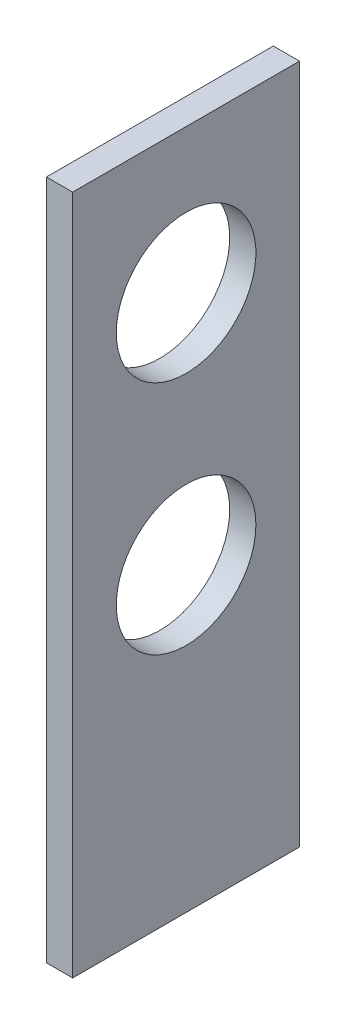
SolidWorks part; units mm, degrees
material "Balsa"
ref_plane "Alzado" through (0, 0, 0) normal (0, 0, 1) x (1, 0, 0)
ref_plane "Planta" through (0, 0, 0) normal (0, 1, 0) x (1, 0, 0)
ref_plane "Vista lateral" through (0, 0, 0) normal (1, 0, 0) x (0, 0, -1)
sketch "Croquis1" plane through (0, 0, 0) normal (1, 0, 0) x (0, 0, -1)
  line L1 (0, 0) -> (-26, 0)
  line L2 (0, 0) -> (0, 78)
  line L3 (0, 78) -> (-26, 78)
  line L4 (-26, 0) -> (-26, 78)
  dimension "D1" = 26
  dimension "D2" = 78
extrude "Saliente-Extruir1" add sketch "Croquis1" along normal blind 3
sketch "Croquis2" plane through (0, 0, 0) normal (-1, 0, 0) x (0, 0, 1)
  line L0 (13, 78) -> (13, 0) construction
  line L1 (0, 78) -> (26, 78) construction
  line L2 (26, 0) -> (0, 0) construction
  line L3 (0, 48) -> (26, 48) construction
  line L4 (0, 0) -> (0, 78) construction
  line L5 (26, 78) -> (26, 0) construction
  circle A0 centre (13, 61.5) radius 8
  circle A1 centre (13, 34.5) radius 8
  dimension "D2" = 16
  dimension "D3" = 27
  dimension "D1" = 48
extrude "Cortar-Extruir1" cut sketch "Croquis2" against normal through all
